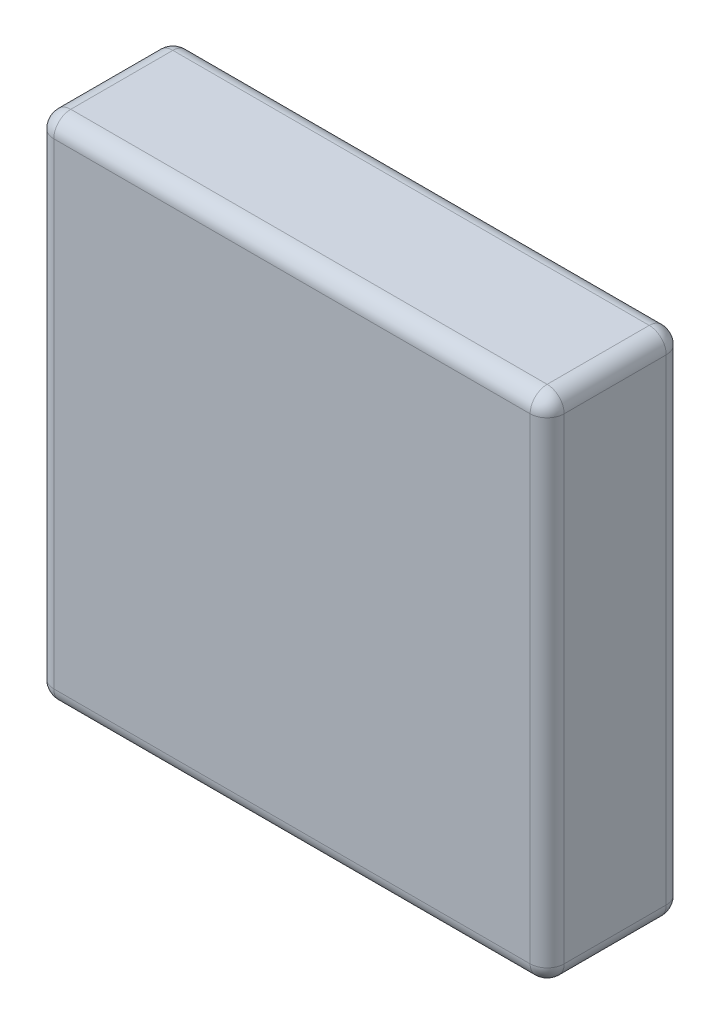
SolidWorks part; units mm, degrees
ref_plane "Front Plane" through (0, 0, 0) normal (0, 0, 1) x (1, 0, 0)
ref_plane "Top Plane" through (0, 0, 0) normal (0, 1, 0) x (1, 0, 0)
ref_plane "Right Plane" through (0, 0, 0) normal (1, 0, 0) x (0, 0, -1)
sketch "Sketch2" plane through (0, 0, 0) normal (0, 0, 1) x (1, 0, 0)
  line L1 (0, 0) -> (30, 0)
  line L2 (0, 0) -> (0, -30)
  line L3 (0, -30) -> (30, -30)
  line L4 (30, 0) -> (30, -30)
  dimension "D1" = 30
extrude "Extrude1" add sketch "Sketch2" along normal blind 8
fillet "Fillet1" radius 1 12 edges at (0, -30, 4) (30, -30, 4) (30, 0, 4) (0, 0, 4) (15, 0, 8) (30, -15, 8) (15, -30, 8) (0, -15, 8) (15, 0, 0) (30, -15, 0) (15, -30, 0) (0, -15, 0)
